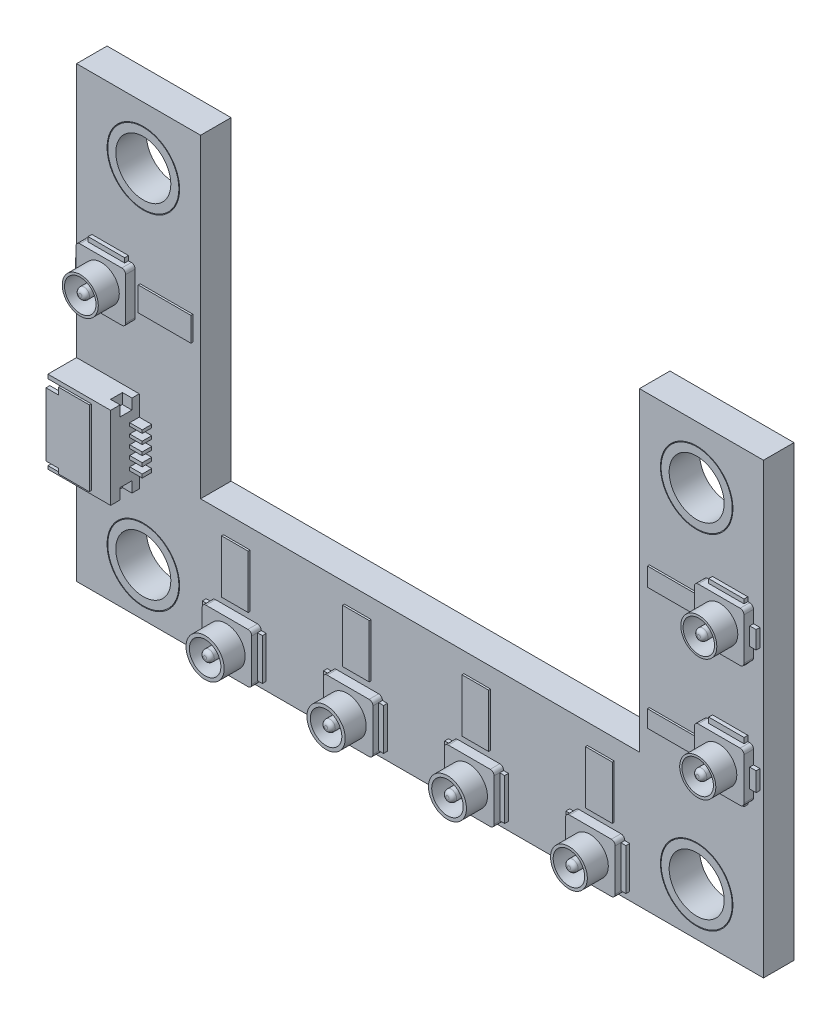
SolidWorks part; units mm, degrees
ref_plane "前视基准面" through (0, 0, 0) normal (0, 0, 1) x (1, 0, 0)
ref_plane "上视基准面" through (0, 0, 0) normal (0, 1, 0) x (1, 0, 0)
ref_plane "右视基准面" through (0, 0, 0) normal (1, 0, 0) x (0, 0, -1)
sketch "草图1" plane through (0, 0, 0) normal (0, 0, 1) x (1, 0, 0)
sketch_block_instance "DXF_ScannerConnector_2023-05-05-4"
sketch_block "DXF_ScannerConnector_2023-05-05"
other "细节项目8"
other "细节项目9"
other "细节项目10"
other "细节项目11"
other "细节项目12"
other "细节项目13"
other "细节项目14"
sketch "草图2" plane through (0, 0, 0) normal (0, 0, 1) x (1, 0, 0)
  line L0 (7.77, 24.892) -> (7.77, 8.392)
  line L1 (7.77, 8.392) -> (30.77, 8.392)
  line L2 (30.77, 8.392) -> (30.77, 24.892)
  line L3 (30.77, 24.892) -> (37.27, 24.892)
  line L4 (37.27, 24.892) -> (37.27, 1.392)
  line L5 (37.27, 1.392) -> (1.27, 1.392)
  line L6 (1.27, 1.392) -> (1.27, 24.892)
  line L7 (1.27, 24.892) -> (7.77, 24.892)
extrude "凸台-拉伸1" add sketch "草图2" along normal blind 1.6
sketch "草图3" plane through (0, 0, 1.6) normal (0, 0, 1) x (1, 0, 0)
  circle A0 centre (4.77, 21.892) radius 1.9
  circle A1 centre (33.7701, 21.892) radius 1.9
  circle A2 centre (33.77, 3.892) radius 1.9
  circle A3 centre (4.77, 3.892) radius 1.9
extrude "切除-拉伸1" cut sketch "草图3" against normal blind 1.6
sketch "草图4" plane through (0, 0, 1.6) normal (0, 0, 1) x (1, 0, 0)
  line L0 (1.27, 24.892) -> (1.27, 1.392) construction
  line L1 (4.5568, 7.2339) -> (1.27, 7.2339)
  line L2 (4.5568, 7.2339) -> (4.5568, 11.55)
  line L3 (4.5568, 11.55) -> (1.27, 11.55)
  line L4 (1.27, 7.2339) -> (1.27, 11.55)
extrude "凸台-拉伸2" add sketch "草图4" along normal blind 1.5
sketch "草图5" plane through (4.5568, 0, 0) normal (1, 0, 0) x (0, 0, -1)
  line L0 (-3.1, 7.2339) -> (-1.6, 7.2339) construction
  line L1 (-2.6052, 7.2339) -> (-1.9826, 7.2339)
  line L2 (-2.6052, 7.2339) -> (-2.6052, 7.7952)
  line L3 (-2.6052, 7.7952) -> (-1.9826, 7.7952)
  line L4 (-1.9826, 7.2339) -> (-1.9826, 7.7952)
  line L5 (-3.1, 11.55) -> (-1.6, 11.55) construction
  line L6 (-2.6052, 11.55) -> (-1.9826, 11.55)
  line L7 (-2.6052, 11.55) -> (-2.6052, 11.0037)
  line L8 (-2.6052, 11.0037) -> (-1.9826, 11.0037)
  line L9 (-1.9826, 11.55) -> (-1.9826, 11.0037)
extrude "切除-拉伸2" cut sketch "草图5" against normal blind 0.5
sketch "草图6" plane through (0, 0, 1.6) normal (0, 0, 1) x (1, 0, 0)
  line L0 (4.5568, 7.2339) -> (4.5568, 11.55) construction
  line L1 (4.5568, 8.486) -> (5.2105, 8.486)
  line L2 (4.5568, 8.486) -> (4.5568, 8.302)
  line L3 (4.5568, 8.302) -> (5.2105, 8.302)
  line L4 (5.2105, 8.486) -> (5.2105, 8.302)
  line L5 (4.5568, 7.2339) -> (4.5568, 11.55) construction
  line L6 (4.5568, 8.9993) -> (5.2105, 8.9993)
  line L7 (4.5568, 8.9993) -> (4.5568, 8.8105)
  line L8 (4.5568, 8.8105) -> (5.2105, 8.8105)
  line L9 (5.2105, 8.9993) -> (5.2105, 8.8105)
  line L10 (4.5568, 9.4888) -> (5.2105, 9.4888)
  line L11 (4.5568, 9.4888) -> (4.5568, 9.3159)
  line L12 (4.5568, 9.3159) -> (5.2105, 9.3159)
  line L13 (5.2105, 9.4888) -> (5.2105, 9.3159)
  line L14 (4.5568, 9.9759) -> (5.2105, 9.9759)
  line L15 (4.5568, 9.9759) -> (4.5568, 9.8164)
  line L16 (4.5568, 9.8164) -> (5.2105, 9.8164)
  line L17 (5.2105, 9.9759) -> (5.2105, 9.8164)
  line L19 (4.5568, 10.49) -> (5.2105, 10.49)
  line L20 (4.5568, 10.49) -> (4.5568, 10.3272)
  line L21 (4.5568, 10.3272) -> (5.2105, 10.3272)
  line L22 (5.2105, 10.49) -> (5.2105, 10.3272)
extrude "凸台-拉伸3" add sketch "草图6" along normal blind 0.5
sketch "草图7" plane through (1.27, 0, 0) normal (-1, 0, 0) x (0, 0, 1)
  line L1 (3.2169, 11.3376) -> (1.7858, 11.3376)
  line L2 (3.2169, 11.3376) -> (3.2169, 7.3963)
  line L3 (3.2169, 7.3963) -> (1.7858, 7.3963)
  line L4 (1.7858, 11.3376) -> (1.7858, 7.3963)
extrude "切除-拉伸3" cut sketch "草图7" against normal blind 2
sketch "草图9" plane through (1.27, 0, 0) normal (-1, 0, 0) x (0, 0, 1)
  line L1 (1.6936, 10.9792) -> (2.9308, 10.9792)
  line L2 (1.6936, 10.9792) -> (1.6936, 10.6709)
  line L3 (1.6936, 10.6709) -> (2.9308, 10.6709)
  line L4 (2.9308, 10.9792) -> (2.9308, 10.6709)
  line L5 (1.6936, 10.2252) -> (2.9308, 10.2252)
  line L6 (1.6936, 10.2252) -> (1.6936, 9.9503)
  line L7 (1.6936, 9.9503) -> (2.9308, 9.9503)
  line L8 (2.9308, 10.2252) -> (2.9308, 9.9503)
  line L9 (1.6853, 9.5254) -> (2.9225, 9.5254)
  line L10 (1.6853, 9.5254) -> (1.6853, 9.213)
  line L11 (1.6853, 9.213) -> (2.9225, 9.213)
  line L12 (2.9225, 9.5254) -> (2.9225, 9.213)
  line L13 (1.6853, 8.8464) -> (2.9225, 8.8464)
  line L14 (1.6853, 8.8464) -> (1.6853, 8.5173)
  line L15 (1.6853, 8.5173) -> (2.9225, 8.5173)
  line L16 (2.9225, 8.8464) -> (2.9225, 8.5173)
  line L17 (1.6894, 8.1924) -> (2.9266, 8.1924)
  line L18 (1.6894, 8.1924) -> (1.6894, 7.9133)
  line L19 (1.6894, 7.9133) -> (2.9266, 7.9133)
  line L20 (2.9266, 8.1924) -> (2.9266, 7.9133)
extrude "切除-拉伸4" cut sketch "草图9" against normal blind 2.5
sketch "草图10" plane through (0, 0, 3.1) normal (0, 0, 1) x (1, 0, 0)
  line L0 (1.9315, 11.3376) -> (1.9315, 10.9792)
  line L1 (3.27, 11.3376) -> (1.27, 11.3376) construction
  line L2 (1.27, 10.9792) -> (3.27, 10.9792) construction
  line L3 (1.9315, 10.9792) -> (1.27, 10.9792)
  line L4 (1.27, 10.9792) -> (1.27, 7.6548)
  line L5 (1.27, 7.9133) -> (1.27, 7.3963) construction
  line L6 (1.27, 7.6548) -> (1.9315, 7.6548)
  line L7 (1.9315, 7.6548) -> (1.9315, 7.3963)
  line L8 (3.27, 7.3963) -> (1.27, 7.3963) construction
  line L9 (1.9315, 7.3963) -> (3.5412, 7.3963)
  line L10 (3.5412, 7.3963) -> (3.5412, 11.3376)
  line L11 (3.5412, 11.3376) -> (1.9315, 11.3376)
extrude "凸台-拉伸6" add sketch "草图10" along normal mid plane 0.2
sketch "草图11" plane through (0, 0, 1.6) normal (0, 0, 1) x (1, 0, 0)
  line L1 (8.3519, 4.2059) -> (10.952, 4.2059)
  line L2 (8.3519, 4.2059) -> (8.3519, 1.606)
  line L3 (8.3519, 1.606) -> (10.952, 1.606)
  line L4 (10.952, 4.2059) -> (10.952, 1.606)
  line L5 (14.7019, 4.2059) -> (17.302, 4.2059)
  line L6 (14.7019, 4.2059) -> (14.7019, 1.606)
  line L7 (14.7019, 1.606) -> (17.302, 1.606)
  line L8 (17.302, 4.2059) -> (17.302, 1.606)
  line L9 (21.0519, 4.2059) -> (23.652, 4.2059)
  line L10 (21.0519, 4.2059) -> (21.0519, 1.606)
  line L11 (21.0519, 1.606) -> (23.652, 1.606)
  line L12 (23.652, 4.2059) -> (23.652, 1.606)
  line L13 (27.402, 4.2059) -> (30.0021, 4.2059)
  line L14 (27.402, 4.2059) -> (27.402, 1.606)
  line L15 (27.402, 1.606) -> (30.0021, 1.606)
  line L16 (30.0021, 4.2059) -> (30.0021, 1.606)
  line L17 (34.1482, 9.1139) -> (36.7481, 9.1139)
  line L18 (34.1482, 9.1139) -> (34.1482, 11.714)
  line L19 (34.1482, 11.714) -> (36.7481, 11.714)
  line L20 (36.7481, 9.1139) -> (36.7481, 11.714)
  line L21 (34.1482, 15.4639) -> (36.7481, 15.4639)
  line L22 (34.1482, 15.4639) -> (34.1482, 18.064)
  line L23 (34.1482, 18.064) -> (36.7481, 18.064)
  line L24 (36.7481, 15.4639) -> (36.7481, 18.064)
  line L25 (4.3429, 17.3033) -> (1.7431, 17.3033)
  line L26 (4.3429, 17.3033) -> (4.3429, 14.7032)
  line L27 (4.3429, 14.7032) -> (1.7431, 14.7032)
  line L28 (1.7431, 17.3033) -> (1.7431, 14.7032)
extrude "凸台-拉伸7" add sketch "草图11" along normal blind 0.5
sketch "草图12" plane through (0, 0, 2.1) normal (0, 0, 1) x (1, 0, 0)
  circle A0 centre (9.608, 2.9019) radius 1.0001
  circle A1 centre (15.9483, 2.9019) radius 1.0037
  circle A2 centre (22.3094, 2.9019) radius 0.9952
  circle A3 centre (28.6751, 2.9019) radius 0.9645
  circle A4 centre (35.4267, 10.4023) radius 0.9462
  circle A5 centre (35.4817, 16.8138) radius 0.9433
  circle A6 centre (3.0653, 16.0732) radius 0.9453
extrude "凸台-拉伸8" add sketch "草图12" along normal blind 1.1
sketch "草图13" plane through (0, 0, 3.2) normal (0, 0, 1) x (1, 0, 0)
  circle A0 centre (9.608, 2.9019) radius 0.8255
  circle A1 centre (9.608, 2.9019) radius 0.281
  circle A2 centre (15.9483, 2.9019) radius 0.8255
  circle A3 centre (15.9483, 2.9019) radius 0.281
  circle A4 centre (22.3094, 2.9019) radius 0.8255
  circle A5 centre (22.3094, 2.9019) radius 0.281
  circle A6 centre (28.6751, 2.9019) radius 0.8255
  circle A7 centre (28.6751, 2.9019) radius 0.281
  circle A8 centre (35.4214, 10.4145) radius 0.8255
  circle A9 centre (35.4214, 10.4145) radius 0.281
  circle A10 centre (35.4818, 16.8028) radius 0.8255
  circle A11 centre (35.4818, 16.8028) radius 0.281
  circle A12 centre (3.0653, 16.0732) radius 0.8255
  circle A13 centre (3.0653, 16.0732) radius 0.281
extrude "切除-拉伸5" cut sketch "草图13" against normal blind 1.1
sketch "草图14" plane through (0, 0, 1.6) normal (0, 0, 1) x (1, 0, 0)
  line L0 (8.3519, 4.2059) -> (8.3519, 1.606) construction
  line L1 (8.3519, 4.0033) -> (8.0627, 4.0033)
  line L2 (8.3519, 4.0033) -> (8.3519, 1.8251)
  line L3 (8.3519, 1.8251) -> (8.0627, 1.8251)
  line L4 (8.0627, 4.0033) -> (8.0627, 1.8251)
  line L5 (10.952, 1.606) -> (10.952, 4.2059) construction
  line L6 (10.952, 1.8251) -> (11.2095, 1.8251)
  line L7 (10.952, 1.8251) -> (10.952, 4.0033)
  line L8 (10.952, 4.0033) -> (11.2095, 4.0033)
  line L9 (11.2095, 1.8251) -> (11.2095, 4.0033)
  line L10 (8.3519, 1.606) -> (10.952, 1.606) construction
  line L11 (9.3638, 1.606) -> (9.9485, 1.606)
  line L12 (9.3638, 1.606) -> (9.3638, 1.4812)
  line L13 (9.3638, 1.4812) -> (9.9485, 1.4812)
  line L14 (9.9485, 1.606) -> (9.9485, 1.4812)
  line L15 (14.6993, 4.0034) -> (14.4101, 4.0034)
  line L16 (14.6993, 4.0034) -> (14.6993, 1.8252)
  line L17 (14.6993, 1.8252) -> (14.4101, 1.8252)
  line L18 (14.4101, 4.0034) -> (14.4101, 1.8252)
  line L19 (17.2995, 1.8252) -> (17.557, 1.8252)
  line L20 (17.2995, 1.8252) -> (17.2995, 4.0034)
  line L21 (17.2995, 4.0034) -> (17.557, 4.0034)
  line L22 (17.557, 1.8252) -> (17.557, 4.0034)
  line L23 (15.7113, 1.6061) -> (16.2959, 1.6061)
  line L24 (15.7113, 1.6061) -> (15.7113, 1.4813)
  line L25 (15.7113, 1.4813) -> (16.2959, 1.4813)
  line L26 (16.2959, 1.6061) -> (16.2959, 1.4813)
  line L27 (21.0499, 3.9982) -> (20.7606, 3.9982)
  line L28 (21.0499, 3.9982) -> (21.0499, 1.82)
  line L29 (21.0499, 1.82) -> (20.7606, 1.82)
  line L30 (20.7606, 3.9982) -> (20.7606, 1.82)
  line L31 (23.65, 1.82) -> (23.9075, 1.82)
  line L32 (23.65, 1.82) -> (23.65, 3.9982)
  line L33 (23.65, 3.9982) -> (23.9075, 3.9982)
  line L34 (23.9075, 1.82) -> (23.9075, 3.9982)
  line L35 (22.0618, 1.6009) -> (22.6465, 1.6009)
  line L36 (22.0618, 1.6009) -> (22.0618, 1.4761)
  line L37 (22.0618, 1.4761) -> (22.6465, 1.4761)
  line L38 (22.6465, 1.6009) -> (22.6465, 1.4761)
  line L39 (27.4037, 3.995) -> (27.1144, 3.995)
  line L40 (27.4037, 3.995) -> (27.4037, 1.8168)
  line L41 (27.4037, 1.8168) -> (27.1144, 1.8168)
  line L42 (27.1144, 3.995) -> (27.1144, 1.8168)
  line L43 (30.0038, 1.8168) -> (30.2613, 1.8168)
  line L44 (30.0038, 1.8168) -> (30.0038, 3.995)
  line L45 (30.0038, 3.995) -> (30.2613, 3.995)
  line L46 (30.2613, 1.8168) -> (30.2613, 3.995)
  line L47 (28.4156, 1.5977) -> (29.0003, 1.5977)
  line L48 (28.4156, 1.5977) -> (28.4156, 1.4729)
  line L49 (28.4156, 1.4729) -> (29.0003, 1.4729)
  line L50 (29.0003, 1.5977) -> (29.0003, 1.4729)
  line L51 (36.7481, 15.4639) -> (36.7481, 18.064) construction
  line L52 (36.7481, 17.2123) -> (37.085, 17.2123)
  line L53 (36.7481, 17.2123) -> (36.7481, 16.2818)
  line L54 (36.7481, 16.2818) -> (37.085, 16.2818)
  line L55 (37.085, 17.2123) -> (37.085, 16.2818)
  line L56 (36.7481, 9.1139) -> (36.7481, 11.714) construction
  line L57 (36.7481, 10.8045) -> (37.085, 10.8045)
  line L58 (36.7481, 10.8045) -> (36.7481, 9.8088)
  line L59 (36.7481, 9.8088) -> (37.085, 9.8088)
  line L60 (37.085, 10.8045) -> (37.085, 9.8088)
  line L61 (36.7481, 11.714) -> (34.1482, 11.714) construction
  line L62 (34.5972, 11.714) -> (36.4516, 11.714)
  line L63 (34.5972, 11.714) -> (34.5972, 11.9994)
  line L64 (34.5972, 11.9994) -> (36.4516, 11.9994)
  line L65 (36.4516, 11.714) -> (36.4516, 11.9994)
  line L66 (34.1482, 9.1139) -> (36.7481, 9.1139) construction
  line L67 (34.5972, 9.1139) -> (36.4516, 9.1139)
  line L68 (34.5972, 9.1139) -> (34.5972, 8.8537)
  line L69 (34.5972, 8.8537) -> (36.4516, 8.8537)
  line L70 (36.4516, 9.1139) -> (36.4516, 8.8537)
  line L71 (36.7481, 18.064) -> (34.1482, 18.064) construction
  line L72 (34.5972, 18.064) -> (36.4516, 18.064)
  line L73 (34.5972, 18.064) -> (34.5972, 18.2841)
  line L74 (34.5972, 18.2841) -> (36.4516, 18.2841)
  line L75 (36.4516, 18.064) -> (36.4516, 18.2841)
  line L76 (34.1482, 15.4639) -> (36.7481, 15.4639) construction
  line L77 (34.5972, 15.4639) -> (36.4516, 15.4639)
  line L78 (34.5972, 15.4639) -> (34.5972, 15.262)
  line L79 (34.5972, 15.262) -> (36.4516, 15.262)
  line L80 (36.4516, 15.4639) -> (36.4516, 15.262)
  line L81 (1.7431, 17.3033) -> (1.7431, 14.7032) construction
  line L82 (1.7431, 16.2818) -> (1.4271, 16.2818)
  line L83 (1.7431, 16.2818) -> (1.7431, 15.7413)
  line L84 (1.7431, 15.7413) -> (1.4271, 15.7413)
  line L85 (1.4271, 16.2818) -> (1.4271, 15.7413)
  line L86 (1.7431, 14.7032) -> (4.3429, 14.7032) construction
  line L87 (2.0758, 14.7032) -> (3.9901, 14.7032)
  line L88 (2.0758, 14.7032) -> (2.0758, 14.4598)
  line L89 (2.0758, 14.4598) -> (3.9901, 14.4598)
  line L90 (3.9901, 14.7032) -> (3.9901, 14.4598)
  line L91 (4.3429, 17.3033) -> (1.7431, 17.3033) construction
  line L92 (2.0758, 17.3033) -> (3.9901, 17.3033)
  line L93 (2.0758, 17.3033) -> (2.0758, 17.5434)
  line L94 (2.0758, 17.5434) -> (3.9901, 17.5434)
  line L95 (3.9901, 17.3033) -> (3.9901, 17.5434)
extrude "凸台-拉伸9" add sketch "草图14" along normal blind 0.2
fillet "圆角1" radius 0.2 28 edges at (36.7481, 11.714, 1.85) (34.1482, 11.714, 1.85) (34.1482, 18.064, 1.85) (36.7481, 18.064, 1.85) (34.1482, 15.4639, 1.85) (36.7481, 15.4639, 1.85) (36.7481, 9.1139, 1.85) (34.1482, 9.1139, 1.85) (27.402, 1.606, 1.85) (27.402, 4.2059, 1.85) (30.0021, 1.606, 1.85) (30.0021, 4.2059, 1.85) (23.652, 4.2059, 1.85) (21.0519, 4.2059, 1.85) (21.0519, 1.606, 1.85) (23.652, 1.606, 1.85) (17.302, 1.606, 1.85) (14.7019, 1.606, 1.85) (17.302, 4.2059, 1.85) (14.7019, 4.2059, 1.85) (10.952, 4.2059, 1.85) (8.3519, 4.2059, 1.85) (8.3519, 1.606, 1.85) (10.952, 1.606, 1.85) (4.3429, 14.7032, 1.85) (1.7431, 14.7032, 1.85) (4.3429, 17.3033, 1.85) (1.7431, 17.3033, 1.85)
fillet "圆角2" radius 0.2 7 edges at (35.7628, 16.8028, 3.2) (35.7023, 10.4145, 3.2) (28.9561, 2.9019, 3.2) (22.5904, 2.9019, 3.2) (16.2293, 2.9019, 3.2) (9.889, 2.9019, 3.2) (3.3462, 16.0732, 3.2)
sketch "草图15" plane through (0, 0, 1.6) normal (0, 0, 1) x (1, 0, 0)
  circle A0 centre (4.77, 21.892) radius 1.8627
  circle A1 centre (4.77, 3.892) radius 1.8627
  circle A2 centre (33.77, 3.892) radius 1.8627
  circle A3 centre (33.7701, 21.892) radius 1.8627
  circle A4 centre (4.77, 21.892) radius 1.4417
  circle A5 centre (4.77, 3.892) radius 1.4417
  circle A6 centre (33.77, 3.892) radius 1.4417
  circle A7 centre (33.7701, 21.892) radius 1.4417
extrude "凸台-拉伸10" add sketch "草图15" against normal through all separate body
sketch "草图16" plane through (0, 0, 1.6) normal (0, 0, 1) x (1, 0, 0)
  line L0 (15.3096, 7.3831) -> (16.7097, 7.3831)
  line L1 (4.6007, 16.5652) -> (7.3656, 16.5652)
  line L2 (4.6007, 16.5652) -> (4.6007, 15.2992)
  line L3 (4.6007, 15.2992) -> (7.3656, 15.2992)
  line L4 (7.3656, 16.5652) -> (7.3656, 15.2992)
  line L5 (31.2899, 17.1525) -> (33.8896, 17.1525)
  line L6 (31.2899, 17.1525) -> (31.2899, 16.1865)
  line L7 (31.2899, 16.1865) -> (33.8896, 16.1865)
  line L8 (33.8896, 17.1525) -> (33.8896, 16.1865)
  line L9 (31.2899, 10.6749) -> (33.8896, 10.6749)
  line L10 (31.2899, 10.6749) -> (31.2899, 9.7871)
  line L11 (31.2899, 9.7871) -> (33.8896, 9.7871)
  line L12 (33.8896, 10.6749) -> (33.8896, 9.7871)
  line L13 (8.9683, 7.3627) -> (10.3684, 7.3627)
  line L14 (8.9683, 7.3627) -> (8.9683, 4.576)
  line L15 (8.9683, 4.576) -> (10.3684, 4.576)
  line L16 (10.3684, 7.3627) -> (10.3684, 4.576)
  line L17 (15.3096, 7.3831) -> (15.3096, 4.5964)
  line L18 (15.3096, 4.5964) -> (16.7097, 4.5964)
  line L19 (16.7097, 7.3831) -> (16.7097, 4.5964)
  line L20 (21.5694, 7.3559) -> (22.9695, 7.3559)
  line L21 (21.5694, 7.3559) -> (21.5694, 4.5692)
  line L22 (21.5694, 4.5692) -> (22.9695, 4.5692)
  line L23 (22.9695, 7.3559) -> (22.9695, 4.5692)
  line L24 (28.0468, 7.3311) -> (29.4469, 7.3311)
  line L25 (28.0468, 7.3311) -> (28.0468, 4.5445)
  line L26 (28.0468, 4.5445) -> (29.4469, 4.5445)
  line L27 (29.4469, 7.3311) -> (29.4469, 4.5445)
extrude "凸台-拉伸11" add sketch "草图16" along normal blind 0.1
